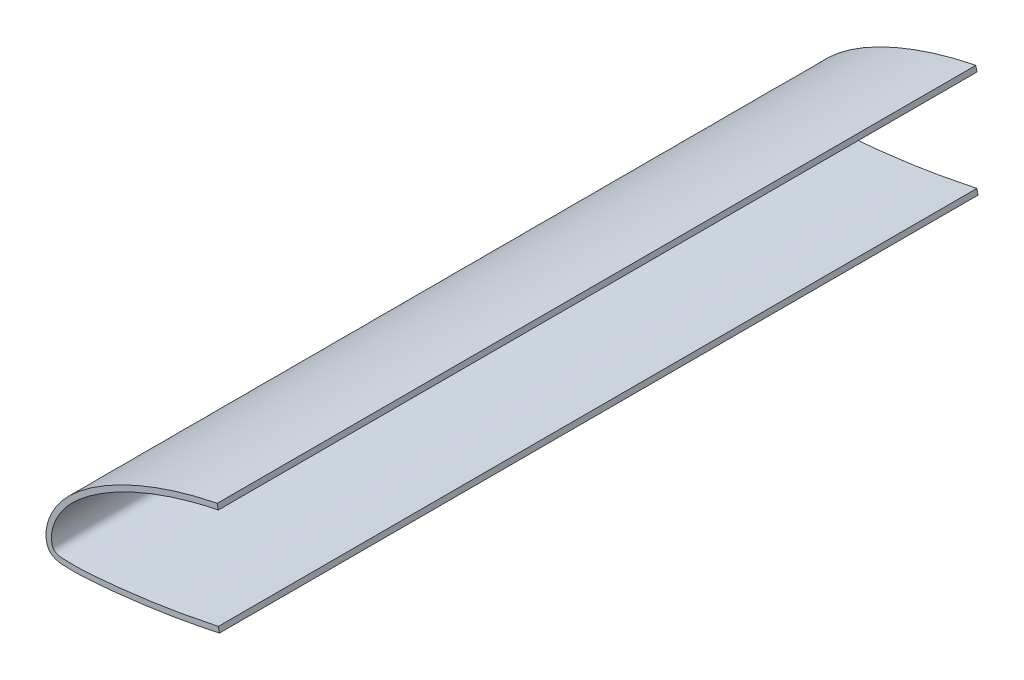
SolidWorks part; units mm, degrees
material "Balsa"
ref_plane "Front Plane" through (0, 0, 0) normal (0, 0, 1) x (1, 0, 0)
ref_plane "Top Plane" through (0, 0, 0) normal (0, 1, 0) x (1, 0, 0)
ref_plane "Right Plane" through (0, 0, 0) normal (1, 0, 0) x (0, 0, -1)
sketch "Sketch1" plane through (0, 0, 0) normal (0, 0, 1) x (1, 0, 0)
  line L0 (0, 37.1065) -> (-0.3855, 39.068)
  line L3 (0, 0) -> (0.4016, -1.9582)
  spline S3 degree 3 poles (0, 37.1065) (-0.5001, 37.0082) (-3.6116, 36.3797) (-9.1885, 35.0573) (-16.5392, 32.9177) (-23.4273, 30.5204) (-29.8241, 27.9195) (-35.6899, 25.1292) (-41.0066, 22.2046) (-45.7453, 19.1787) (-49.8768, 16.0919) (-53.4, 13.0085) (-56.263, 9.896) (-58.4523, 6.7813) (-60.0595, 3.7583) (-61.0769, 0.895) (-61.5443, -1.7413) (-61.4167, -3.9639) (-60.8162, -5.9957) (-58.6741, -6.9791) (-55.8107, -7.082) (-51.8943, -7.1661) (-46.9745, -6.8864) (-41.1045, -6.4159) (-34.3505, -5.6985) (-26.7814, -4.7493) (-18.4346, -3.5506) (-9.4242, -1.9295) (-3.206, -0.6574) (0, 0) knots 0.390259 0.390259 0.390259 0.390259 0.392653 0.40517 0.417172 0.428604 0.439419 0.449597 0.459102 0.467908 0.475988 0.483309 0.489875 0.495803 0.501149 0.505903 0.510047 0.513579 0.516447 0.51935 0.523823 0.529974 0.537716 0.546968 0.557637 0.56962 0.582804 0.597247 0.612622 0.612622 0.612622 0.612622
  spline S4 degree 1 poles (-0.3855, 39.068) (0.4016, -1.9582) knots 0 0 1 1 construction
  spline S5 degree 3 poles (-0.3855, 39.068) (-3.3275, 38.4898) (-9.1775, 37.1479) (-17.8149, 34.6349) (-26.2923, 31.6007) (-34.5717, 27.9872) (-41.2234, 24.4223) (-46.3421, 21.1676) (-50.042, 18.4919) (-53.5762, 15.5705) (-56.8942, 12.2769) (-59.3019, 9.1313) (-60.928, 6.4119) (-61.9868, 4.2449) (-62.8261, 1.9478) (-63.3041, -0.0911) (-63.4791, -1.8195) (-63.4683, -3.1576) (-63.3287, -4.2642) (-63.1147, -5.2248) (-62.8371, -6.0342) (-62.3592, -6.9039) (-61.5831, -7.6945) (-60.7886, -8.1848) (-59.7498, -8.6259) (-58.5646, -8.9048) (-57.2367, -9.0342) (-56.0874, -9.0655) (-54.6029, -9.1066) (-52.6986, -9.1309) (-50.4026, -9.0746) (-48.1446, -8.9507) (-45.914, -8.7974) (-42.9391, -8.5675) (-39.2263, -8.2271) (-34.787, -7.7468) (-30.3592, -7.2144) (-24.4682, -6.4441) (-17.0967, -5.3578) (-8.3041, -3.7407) (-2.5033, -2.5539) (0.4016, -1.9582) knots 0.390259 0.390259 0.390259 0.390259 0.404157 0.418054 0.431952 0.44585 0.459747 0.466696 0.473645 0.480594 0.487543 0.494491 0.497966 0.50144 0.504915 0.508389 0.510126 0.511864 0.513601 0.514469 0.515338 0.516207 0.517075 0.517944 0.518812 0.52055 0.522287 0.524024 0.525761 0.529236 0.53271 0.536184 0.539659 0.543133 0.550082 0.557031 0.56398 0.570929 0.584826 0.598724 0.612622 0.612622 0.612622 0.612622
  dimension "D1" = 1.999
extrude "Boss-Extrude1" add sketch "Sketch1" along normal blind 279.4
